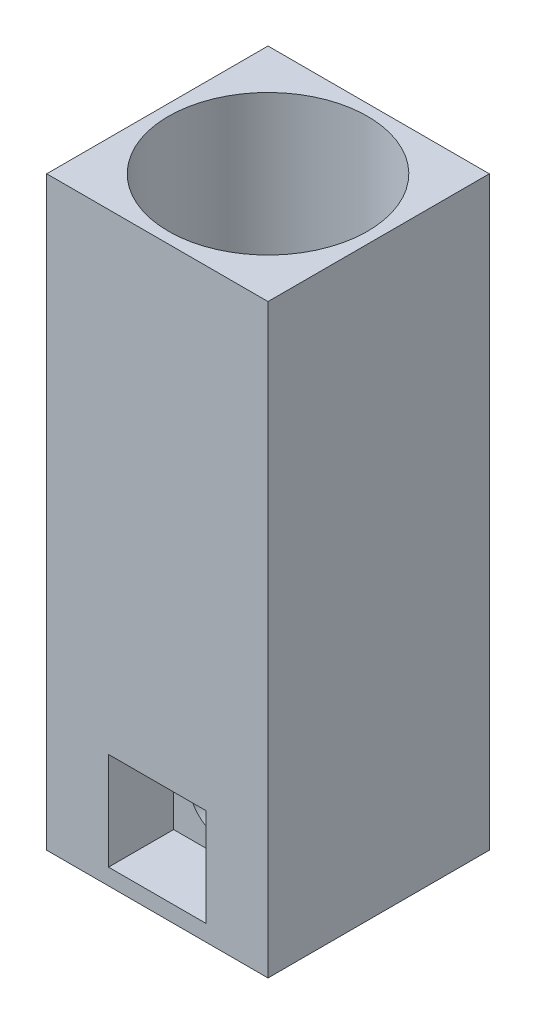
SolidWorks part; units mm, degrees
ref_plane "Front Plane" through (0, 0, 0) normal (0, 0, 1) x (1, 0, 0)
ref_plane "Top Plane" through (0, 0, 0) normal (0, 1, 0) x (1, 0, 0)
ref_plane "Right Plane" through (0, 0, 0) normal (1, 0, 0) x (0, 0, -1)
sketch "Sketch1" plane through (0, 0, 0) normal (0, 1, 0) x (1, 0, 0)
  line L1 (-10.795, -10.795) -> (10.795, -10.795)
  line L2 (-10.795, -10.795) -> (-10.795, 10.795)
  line L3 (-10.795, 10.795) -> (10.795, 10.795)
  line L4 (10.795, -10.795) -> (10.795, 10.795)
  line L5 (-10.795, -10.795) -> (10.795, 10.795) construction
  line L6 (-10.795, 10.795) -> (10.795, -10.795) construction
  point P0 (0, 0)
  dimension "D1" = 21.59
extrude "Boss-Extrude1" add sketch "Sketch1" along normal blind 57.15
sketch "Sketch2" plane through (0, 0, 10.795) normal (0, 0, 1) x (1, 0, 0)
  line L0 (-10.795, 0) -> (10.795, 0) construction
  line L1 (-4.7625, 1.5875) -> (4.7625, 1.5875)
  line L2 (-4.7625, 1.5875) -> (-4.7625, 11.1125)
  line L3 (-4.7625, 11.1125) -> (4.7625, 11.1125)
  line L4 (4.7625, 1.5875) -> (4.7625, 11.1125)
  line L5 (-4.7625, 1.5875) -> (4.7625, 11.1125) construction
  line L6 (-4.7625, 11.1125) -> (4.7625, 1.5875) construction
  point P0 (0, 6.35)
  dimension "D1" = 9.525
  dimension "D2" = 6.35
extrude "Cut-Extrude1" cut sketch "Sketch2" against normal blind 6.35
sketch "Sketch3" plane through (0, 0, 4.445) normal (0, 0, 1) x (1, 0, 0)
  line L0 (-4.7625, 11.1125) -> (4.7625, 1.5875) construction
  line L1 (4.7625, 11.1125) -> (-4.7625, 1.5875) construction
  circle A0 centre (0, 6.35) radius 3.302
  dimension "D1" = 6.604
extrude "Cut-Extrude2" cut sketch "Sketch3" against normal through all contours A0
sketch "Sketch4" plane through (0, 57.15, 0) normal (0, 1, 0) x (1, 0, 0)
  circle A0 centre (0, 0) radius 9.7155
  dimension "D1" = 19.431
extrude "Cut-Extrude3" cut sketch "Sketch4" against normal blind 31.75
